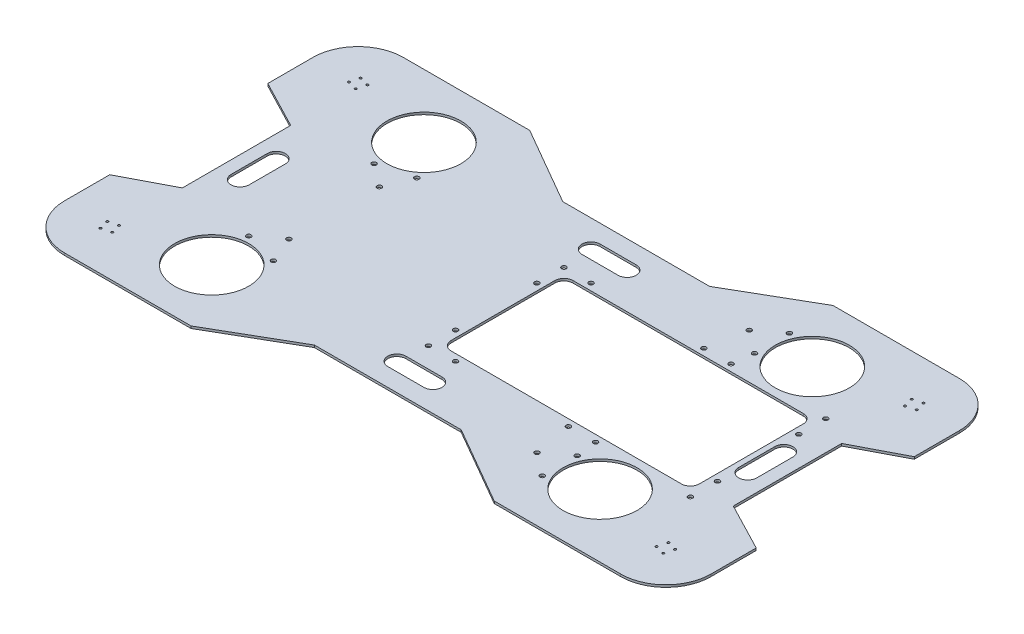
SolidWorks part; units mm, degrees
material "6061 Alloy"
ref_plane "Front Plane" through (0, 0, 0) normal (0, 0, 1) x (1, 0, 0)
ref_plane "Top Plane" through (0, 0, 0) normal (0, 1, 0) x (1, 0, 0)
ref_plane "Right Plane" through (0, 0, 0) normal (1, 0, 0) x (0, 0, -1)
sketch "Sketch1" plane through (0, 0, 0) normal (0, 1, 0) x (1, 0, 0)
  line L44 (387.35, 76.2) -> (387.35, -76.2)
  line L53 (390.996, 174.625) -> (382.7688, 179.375) construction
  line L54 (273.05, 149.225) -> (-273.05, 149.225) construction
  line L55 (-12.7, 85.725) -> (336.55, 85.725) construction
  line L56 (-12.7, 85.725) -> (-12.7, -85.725) construction
  line L57 (-12.7, -85.725) -> (336.55, -85.725) construction
  line L58 (336.55, 85.725) -> (336.55, -85.725) construction
  line L59 (-103.2108, 174.625) -> (103.2108, 174.625)
  line L60 (-454.496, 174.625) -> (-454.496, 111.125)
  line L63 (-103.2108, -174.625) -> (103.2108, -174.625)
  line L64 (273.05, 149.225) -> (273.05, -149.225) construction
  line L65 (-209.55, 139.7) -> (-31.75, 139.7) construction
  line L66 (-209.55, 139.7) -> (-209.55, -139.7) construction
  line L67 (-209.55, -139.7) -> (-31.75, -139.7) construction
  line L68 (-31.75, 139.7) -> (-31.75, -139.7) construction
  line L69 (273.05, -149.225) -> (-273.05, -149.225) construction
  line L70 (-273.05, 149.225) -> (-273.05, -149.225) construction
  line L71 (0, 0) -> (414.6005, 0) construction
  line L72 (454.496, 174.625) -> (454.496, 111.125)
  line L76 (454.496, 111.125) -> (387.35, 76.2)
  line L77 (454.496, -174.625) -> (454.496, -111.125)
  line L81 (454.496, -111.125) -> (387.35, -76.2)
  line L82 (0, 174.625) -> (0, -174.625) construction
  line L83 (-454.496, 111.125) -> (-387.35, 76.2)
  line L84 (-387.35, 76.2) -> (-387.35, -76.2)
  line L85 (-387.35, -76.2) -> (-454.496, -111.125)
  line L86 (-454.496, -111.125) -> (-454.496, -174.625)
  line L87 (-390.996, 174.625) -> (-399.2233, 169.875) construction
  line L88 (-390.996, 238.125) -> (-213.196, 238.125)
  line L89 (-213.196, 238.125) -> (-103.2108, 174.625)
  line L90 (390.996, 238.125) -> (213.196, 238.125)
  line L91 (213.196, 238.125) -> (103.2108, 174.625)
  line L92 (-390.996, -238.125) -> (-213.196, -238.125)
  line L93 (-213.196, -238.125) -> (-103.2108, -174.625)
  line L94 (390.996, -238.125) -> (213.196, -238.125)
  line L95 (213.196, -238.125) -> (103.2108, -174.625)
  arc A8 (454.496, 174.625) -> (390.996, 238.125) centre (390.996, 174.625) ccw
  arc A9 (390.996, -238.125) -> (454.496, -174.625) centre (390.996, -174.625) ccw
  arc A10 (-454.496, -174.625) -> (-390.996, -238.125) centre (-390.996, -174.625) ccw
  arc A11 (-390.996, 238.125) -> (-454.496, 174.625) centre (-390.996, 174.625) ccw
  circle A12 centre (273.05, 149.225) radius 52.07
  circle A13 centre (273.05, -149.225) radius 52.07
  circle A14 centre (-273.05, 149.225) radius 52.07
  circle A15 centre (-273.05, -149.225) radius 52.07
  circle A16 centre (382.7688, 179.375) radius 1.575
  circle A17 centre (395.746, 182.8522) radius 1.575
  circle A18 centre (399.2233, 169.875) radius 1.575
  circle A19 centre (386.246, 166.3978) radius 1.575
  circle A20 centre (386.246, -166.3978) radius 1.575
  circle A21 centre (399.2233, -169.875) radius 1.575
  circle A22 centre (395.746, -182.8522) radius 1.575
  circle A23 centre (382.7688, -179.375) radius 1.575
  arc A24 (395.3742, -237.9739) -> (454.496, -174.625) centre (390.996, -174.625) cw construction
  arc A25 (395.3742, 237.9739) -> (454.496, 174.625) centre (390.996, 174.625) ccw construction
  circle A26 centre (-399.2233, 169.875) radius 1.575
  circle A27 centre (-395.746, 182.8522) radius 1.575
  circle A28 centre (-382.7688, 179.375) radius 1.575
  circle A29 centre (-386.246, 166.3978) radius 1.575
  circle A30 centre (-386.246, -166.3978) radius 1.575
  circle A31 centre (-399.2233, -169.875) radius 1.575
  circle A32 centre (-382.7688, -179.375) radius 1.575
  circle A33 centre (-395.746, -182.8522) radius 1.575
  point P0 (0, 0)
  point P13 (-12.7, 0)
  point P16 (-31.75, 0)
  point P43 (390.996, 174.625)
  point P56 (-387.35, 0)
  point P60 (0, 0)
  point P63 (387.35, 0)
  point P69 (336.55, 0)
  point P73 (273.05, 0)
  point P77 (-390.996, 174.625)
  point P99 (0, 174.625)
  dimension "D1" = 127
  dimension "D4" = 279.4
  dimension "D5" = 177.8
  dimension "D6" = 104.14
  dimension "D7" = 9.5
  dimension "D8" = 4
  dimension "D16" = 152.4
  dimension "D22" = 4
  dimension "D24" = 3.15
  dimension "D2" = 349.25
  dimension "D3" = 171.45
  dimension "D9" = 30
  dimension "D10" = 88.9
  dimension "D11" = 63.5
  dimension "D12" = 120.65
  dimension "D13" = 50.8
  dimension "D14" = 63.5
  dimension "D15" = 63.5
  dimension "D17" = 120.65
  dimension "D18" = 19.05
  dimension "D19" = 63.5
  dimension "D20" = 114.3
  dimension "D21" = 9.5
  dimension "D23" = 30
  dimension "D25" = 177.8
  dimension "D26" = 150
extrude "Boss-Extrude1" add sketch "Sketch1" along normal blind 3.175 contours A9 L77 L81 L44 L76 L72 A8 L90 L91 L59 L89 L88 A11 L60 L83 L84 L85 L86 A10 L92 L93 L63 L95 L94
sketch "Sketch2" plane through (0, 3.175, 0) normal (0, 1, 0) x (1, 0, 0)
  line L0 (387.35, -76.2) -> (387.35, 76.2) construction
  line L1 (-12.7, 85.725) -> (336.55, 85.725) construction
  line L2 (-12.7, 85.725) -> (-12.7, -85.725) construction
  line L3 (-12.7, -85.725) -> (336.55, -85.725) construction
  line L4 (336.55, 85.725) -> (336.55, -85.725) construction
  line L5 (336.55, 85.725) -> (346.075, 95.25) construction
  line L6 (346.075, 57.15) -> (336.55, 57.15) construction
  line L7 (-12.7, 0) -> (336.55, 0) construction
  line L9 (0, 85.725) -> (323.85, 85.725)
  line L10 (-12.7, 73.025) -> (-12.7, -73.025)
  line L11 (0, -85.725) -> (323.85, -85.725)
  line L12 (336.55, 73.025) -> (336.55, -73.025)
  circle A0 centre (346.075, 95.25) radius 3.2639
  circle A1 centre (346.075, 57.15) radius 3.2639
  circle A2 centre (212.725, 95.25) radius 3.2639
  circle A3 centre (174.625, 95.25) radius 3.2639
  circle A4 centre (15.875, 95.25) radius 3.2639
  circle A5 centre (-22.225, 95.25) radius 3.2639
  circle A6 centre (-22.225, 57.15) radius 3.2639
  circle A7 centre (346.075, -57.15) radius 3.2639
  circle A8 centre (346.075, -95.25) radius 3.2639
  circle A9 centre (212.725, -95.25) radius 3.2639
  circle A10 centre (174.625, -95.25) radius 3.2639
  circle A11 centre (15.875, -95.25) radius 3.2639
  circle A12 centre (-22.225, -95.25) radius 3.2639
  circle A13 centre (-22.225, -57.15) radius 3.2639
  arc A14 (-12.7, -73.025) -> (0, -85.725) centre (0, -73.025) ccw
  arc A15 (323.85, -85.725) -> (336.55, -73.025) centre (323.85, -73.025) ccw
  arc A16 (323.85, 85.725) -> (336.55, 73.025) centre (323.85, 73.025) cw
  arc A17 (0, 85.725) -> (-12.7, 73.025) centre (0, 73.025) ccw
  point P4 (336.55, 0)
  point P7 (387.35, 0)
  dimension "D4" = 9.525
  dimension "D5" = 6.5278
  dimension "D8" = 38.1
  dimension "D10" = 38.1
  dimension "D13" = 12.7
  dimension "D1" = 349.25
  dimension "D2" = 171.45
  dimension "D3" = 50.8
  dimension "D6" = 38.1
  dimension "D7" = 45
  dimension "D9" = 133.35
  dimension "D11" = 38.1
  dimension "D12" = 9.525
extrude "Cut-Extrude1" cut sketch "Sketch2" against normal through all
sketch "Sketch3" plane through (0, 3.175, 0) normal (0, 1, 0) x (1, 0, 0)
  line L0 (0, 0) -> (50000, 0) construction
  line L1 (273.05, 149.225) -> (-273.05, 149.225) construction
  line L2 (-273.05, 149.225) -> (-256.67, 88.094) construction
  line L3 (-273.05, 149.225) -> (-273.05, -149.225) construction
  line L4 (216.3365, 173.7595) -> (209.7625, 149.225) construction
  line L6 (209.7625, 149.225) -> (216.3365, 124.6905) construction
  line L7 (-282.07, 88.094) -> (-256.67, 88.094) construction
  line L8 (-256.67, 88.094) -> (-234.6729, 100.794) construction
  line L9 (-282.07, 88.094) -> (-234.6729, 100.794) construction
  circle A0 centre (184.3625, 149.225) radius 3.2639
  circle A3 centre (-250.096, 63.5595) radius 3.2639
  circle A8 centre (184.3625, -149.225) radius 3.2639
  circle A10 centre (-250.096, -63.5595) radius 3.2639
  circle A12 centre (216.3365, 173.7595) radius 3.2639
  circle A13 centre (216.3365, 124.6905) radius 3.2639
  circle A14 centre (-282.07, 88.094) radius 3.2639
  circle A15 centre (-234.6729, 100.794) radius 3.2639
  circle A16 centre (216.3365, -124.6905) radius 3.2639
  circle A17 centre (216.3365, -173.7595) radius 3.2639
  circle A18 centre (-234.6729, -100.794) radius 3.2639
  circle A19 centre (-282.07, -88.094) radius 3.2639
  point P27 (-256.67, 88.094)
  dimension "D7" = 6.5278
  dimension "D1" = 6.5278
  dimension "D5" = 63.2875
  dimension "D6" = 15
  dimension "D9" = 25.4
  dimension "D2" = 150
  dimension "D3" = 25.4
  dimension "D4" = 25.4
  dimension "D10" = 63.2875
  dimension "D8" = 150
  dimension "D11" = 25.4
extrude "Cut-Extrude2" cut sketch "Sketch3" against normal through all
sketch "Sketch4" plane through (0, 3.175, 0) normal (0, 1, 0) x (1, 0, 0)
  line L0 (-356.87, 25.4) -> (-356.87, -25.4) construction
  line L3 (-387.35, 0) -> (387.35, 0) construction
  line L4 (387.35, -76.2) -> (387.35, 76.2) construction
  line L5 (0, 174.625) -> (0, -174.625) construction
  line L6 (103.2108, 174.625) -> (-103.2108, 174.625) construction
  line L7 (-103.2108, -174.625) -> (103.2108, -174.625) construction
  line L8 (-344.17, 25.4) -> (-344.17, -25.4)
  line L11 (-369.57, 25.4) -> (-369.57, -25.4)
  line L12 (-387.35, 76.2) -> (-387.35, -76.2) construction
  line L13 (356.87, 25.4) -> (356.87, -25.4) construction
  line L14 (344.17, 25.4) -> (344.17, -25.4)
  line L15 (369.57, 25.4) -> (369.57, -25.4)
  arc A4 (-344.17, 25.4) -> (-369.57, 25.4) centre (-356.87, 25.4) ccw
  arc A5 (-369.57, -25.4) -> (-344.17, -25.4) centre (-356.87, -25.4) ccw
  arc A6 (344.17, 25.4) -> (369.57, 25.4) centre (356.87, 25.4) cw
  arc A7 (369.57, -25.4) -> (344.17, -25.4) centre (356.87, -25.4) cw
  point P2 (-356.87, 0)
  point P22 (356.87, 0)
  dimension "D2" = 12.7
  dimension "D1" = 50.8
  dimension "D3" = 30.48
sketch "Sketch5" plane through (0, 3.175, 0) normal (0, 1, 0) x (1, 0, 0)
  line L0 (-25.4, 136.525) -> (25.4, 136.525) construction
  line L1 (-25.4, 149.225) -> (25.4, 149.225)
  line L2 (-25.4, 123.825) -> (25.4, 123.825)
  line L3 (-387.35, 0) -> (387.35, 0) construction
  line L4 (-387.35, 76.2) -> (-387.35, -76.2) construction
  line L5 (0, 174.625) -> (0, -174.625) construction
  line L6 (103.2108, 174.625) -> (-103.2108, 174.625) construction
  line L7 (387.35, -76.2) -> (387.35, 76.2) construction
  line L8 (-25.4, -136.525) -> (25.4, -136.525) construction
  line L9 (-25.4, -149.225) -> (25.4, -149.225)
  line L10 (-25.4, -123.825) -> (25.4, -123.825)
  arc A0 (-25.4, 149.225) -> (-25.4, 123.825) centre (-25.4, 136.525) ccw
  arc A1 (25.4, 123.825) -> (25.4, 149.225) centre (25.4, 136.525) ccw
  arc A2 (-25.4, -149.225) -> (-25.4, -123.825) centre (-25.4, -136.525) cw
  arc A3 (25.4, -123.825) -> (25.4, -149.225) centre (25.4, -136.525) cw
  point P2 (0, 136.525)
  point P19 (0, -136.525)
  dimension "D1" = 12.7
  dimension "D2" = 38.1
  dimension "D3" = 50.8
extrude "Cut-Extrude3" cut sketch "Sketch4" against normal through all
extrude "Cut-Extrude4" cut sketch "Sketch5" against normal through all
equation "\"T-Offset\"= 49mm + 9 / 16in"
equation "\"D5@Sketch3\"=\"T-Offset\""
equation "\"D10@Sketch3\"=\"T-Offset\""
